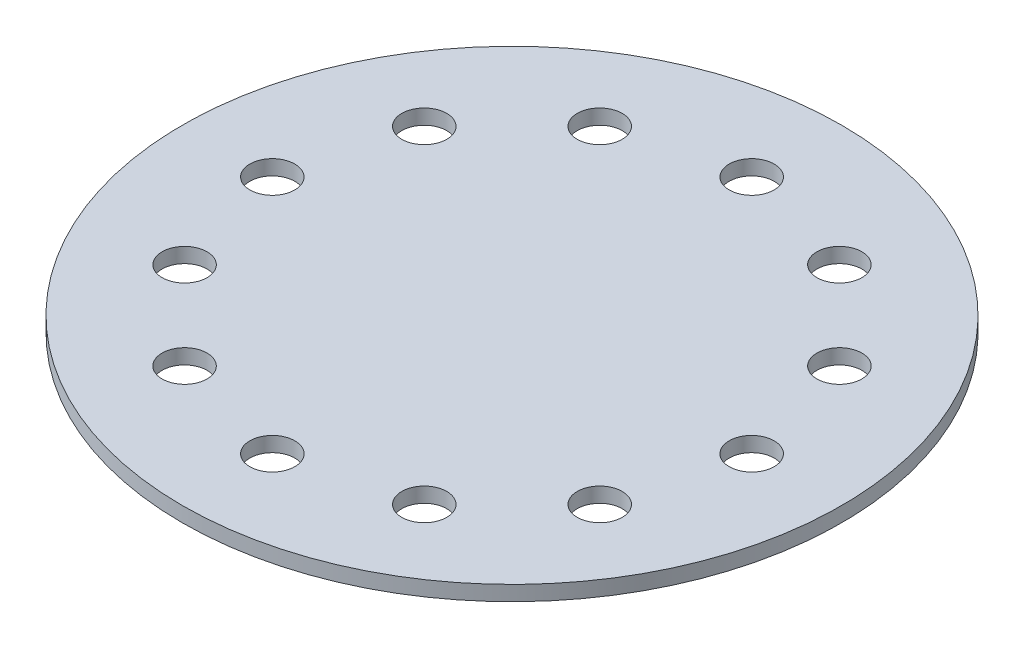
SolidWorks part; units mm, degrees
ref_plane "Front Plane" through (0, 0, 0) normal (0, 0, 1) x (1, 0, 0)
ref_plane "Top Plane" through (0, 0, 0) normal (0, 1, 0) x (1, 0, 0)
ref_plane "Right Plane" through (0, 0, 0) normal (1, 0, 0) x (0, 0, -1)
sketch "Sketch1" plane through (0, 0, 0) normal (0, 1, 0) x (1, 0, 0)
  circle A0 centre (0, 0) radius 22
  circle A1 centre (0, 16) radius 1.5
  circle A2 centre (8, 13.8564) radius 1.5
  circle A3 centre (13.8564, 8) radius 1.5
  circle A4 centre (16, 0) radius 1.5
  circle A5 centre (13.8564, -8) radius 1.5
  circle A6 centre (8, -13.8564) radius 1.5
  circle A7 centre (0, -16) radius 1.5
  circle A8 centre (-8, -13.8564) radius 1.5
  circle A9 centre (-13.8564, -8) radius 1.5
  circle A10 centre (-16, 0) radius 1.5
  circle A11 centre (-13.8564, 8) radius 1.5
  circle A12 centre (-8, 13.8564) radius 1.5
  point P29 (0, 0)
  dimension "D1" = 44
  dimension "D3" = 3
  dimension "D2" = 16
  dimension "D4" = 12
extrude "Boss-Extrude1" add sketch "Sketch1" along normal blind 1
